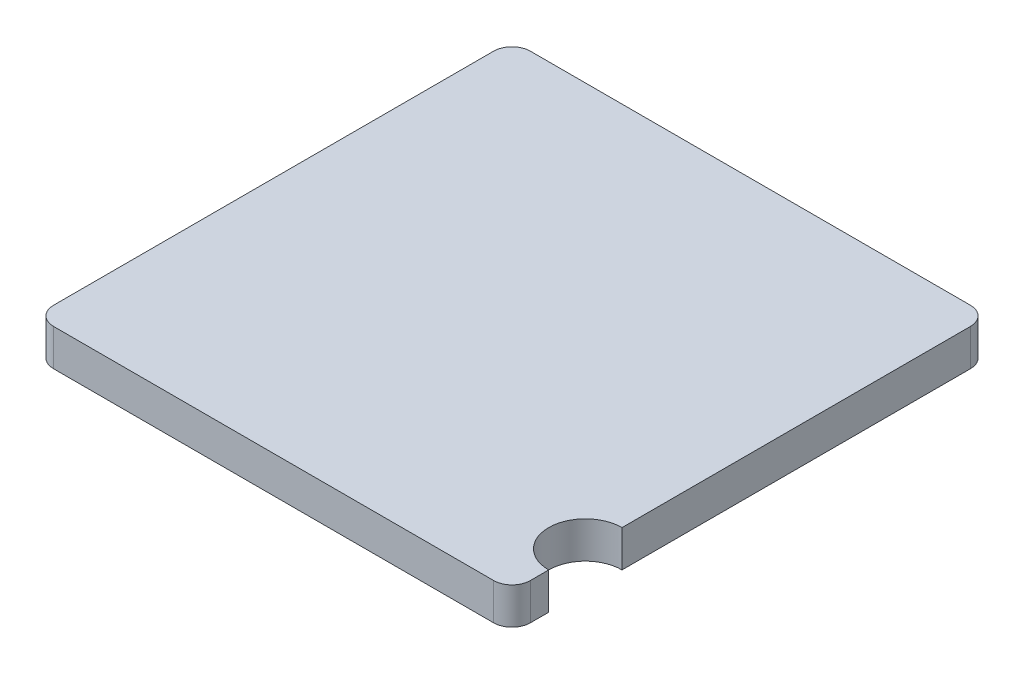
SolidWorks part; units mm, degrees
ref_plane "Front Plane" through (0, 0, 0) normal (0, 0, 1) x (1, 0, 0)
ref_plane "Top Plane" through (0, 0, 0) normal (0, 1, 0) x (1, 0, 0)
ref_plane "Right Plane" through (0, 0, 0) normal (1, 0, 0) x (0, 0, -1)
sketch "Sketch1" plane through (0, 0, 0) normal (0, 1, 0) x (1, 0, 0)
  line L1 (-1.3, 1.3) -> (1.3, 1.3)
  line L2 (-1.3, 1.3) -> (-1.3, -1.3)
  line L3 (-1.3, -1.3) -> (1.3, -1.3)
  line L4 (1.3, 1.3) -> (1.3, -1.3)
  line L5 (-1.3, 1.3) -> (1.3, -1.3) construction
  line L6 (-1.3, -1.3) -> (1.3, 1.3) construction
  point P0 (0, 0)
  dimension "D1" = 2.6
extrude "Boss-Extrude1" add sketch "Sketch1" along normal blind 0.2
fillet "Fillet1" radius 0.1 4 edges at (-1.3, 0.1, -1.3) (1.3, 0.1, -1.3) (1.3, 0.1, 1.3) (-1.3, 0.1, 1.3)
sketch "Sketch3" plane through (0, 0, 0) normal (0, -1, 0) x (1, 0, 0)
  line L0 (1.3, 1.2) -> (1.3, -1.2) construction
  line L1 (-1.2, 1.3) -> (1.2, 1.3) construction
  circle A0 centre (1.3, 0.9) radius 0.2
  dimension "D1" = 0.4
  dimension "D2" = 0.4
extrude "Cut-Extrude1" cut sketch "Sketch3" against normal through all
